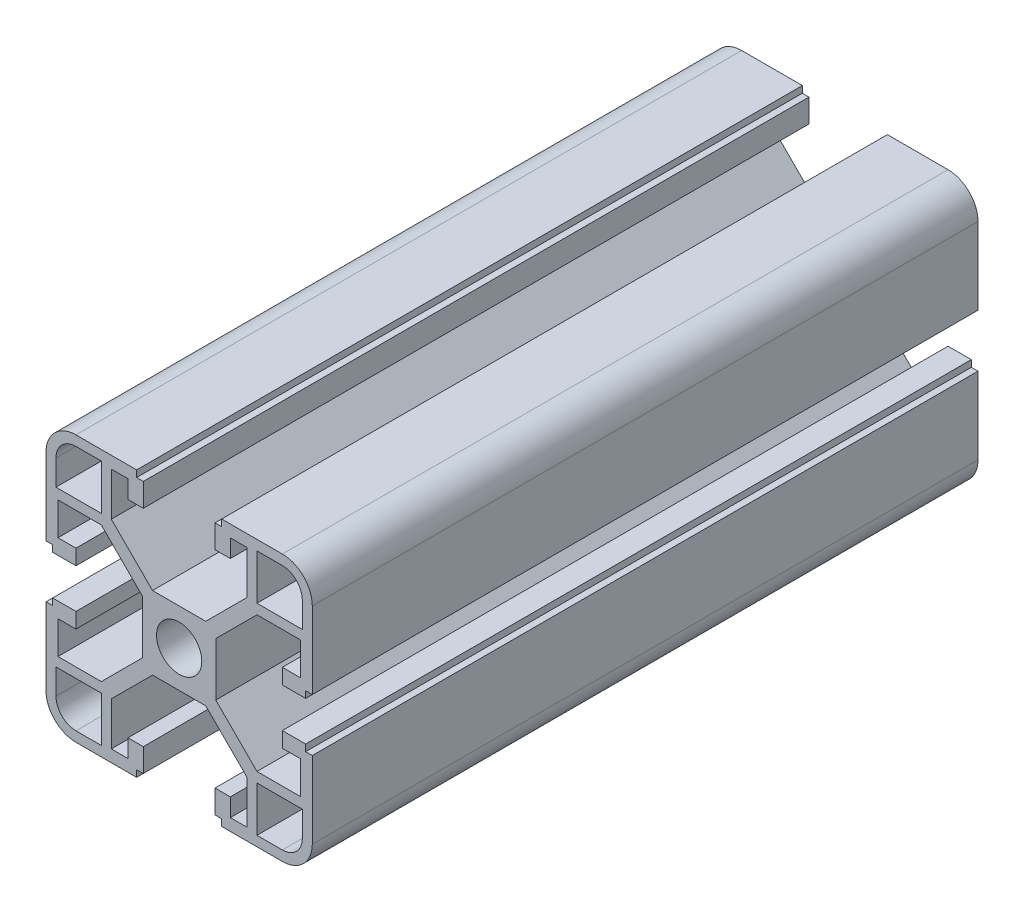
SolidWorks part; units mm, degrees
material "6061-T6 (SS)"
ref_plane "Front Plane" through (0, 0, 0) normal (0, 0, 1) x (1, 0, 0)
ref_plane "Top Plane" through (0, 0, 0) normal (0, 1, 0) x (1, 0, 0)
ref_plane "Right Plane" through (0, 0, 0) normal (1, 0, 0) x (0, 0, -1)
sketch "Sketch1" plane through (0, 0, 0) normal (0, 0, 1) x (1, 0, 0)
  line L0 (3.4, 0) -> (5.5, 0)
  line L1 (10.19, 11.69) -> (4, 5.5)
  line L2 (11.69, 10.19) -> (5.5, 4)
  line L3 (18.2, 10.19) -> (11.69, 10.19)
  line L4 (18.2, 10.19) -> (18.2, 5.2656)
  line L5 (18.2, 5.2656) -> (15.5, 5.2656)
  line L6 (15.5, 5.2656) -> (15.5, 2.9656)
  line L7 (15.5, 2.9656) -> (19, 2.9656)
  line L8 (19, 2.9656) -> (19, 3.9656)
  line L9 (19, 3.9656) -> (20, 3.9656)
  line L10 (20, 3.9656) -> (20, 15.5)
  line L11 (15.5, 20) -> (6.3853, 20)
  line L12 (18.5, 11.69) -> (18.5, 15.5)
  line L13 (15.5, 18.5) -> (11.69, 18.5)
  line L14 (11.69, 11.69) -> (11.69, 18.5)
  line L15 (0, 3.4) -> (0, 5.5)
  line L16 (4, 5.5) -> (0, 5.5)
  line L17 (6.3853, 20) -> (6.3853, 19)
  line L18 (5.5, 0) -> (5.5, 4)
  line L19 (6.3853, 19) -> (5.3853, 19)
  line L20 (5.3853, 19) -> (5.3853, 15.5)
  line L21 (5.3853, 15.5) -> (7.6853, 15.5)
  line L22 (10.19, 11.69) -> (10.19, 18.2)
  line L23 (11.69, 11.69) -> (18.5, 11.69)
  line L24 (7.6853, 18.2) -> (7.6853, 15.5)
  line L25 (10.19, 18.2) -> (7.6853, 18.2)
  arc A0 (20, 15.5) -> (15.5, 20) centre (15.5, 15.5) ccw
  arc A1 (18.5, 15.5) -> (15.5, 18.5) centre (15.5, 15.5) ccw
  arc A2 (3.4, 0) -> (0, 3.4) centre (0, 0) ccw
  dimension "D3" = 4.5
  dimension "D18" = 1.5
  dimension "D9" = 3.4
  dimension "D20" = 1.8
  dimension "D25" = 3
  dimension "D1" = 5.5
  dimension "D2" = 1.5
  dimension "D4" = 14.5
  dimension "D5" = 1.5
  dimension "D6" = 2.1
  dimension "D7" = 2.3
  dimension "D8" = 1.8
  dimension "D10" = 6.81
  dimension "D11" = 2.1
  dimension "D12" = 1
  dimension "D13" = 4.5
  dimension "D14" = 45
  dimension "D15" = 14.5
  dimension "D16" = 1
  dimension "D17" = 1.5
  dimension "D19" = 6.81
  dimension "D21" = 4.5
  dimension "D22" = 2.3
  dimension "D23" = 1
  dimension "D24" = 1
  dimension "D26" = 8.754
  dimension "D27" = 8.754
  dimension "D28" = 4.9244
  dimension "D29" = 2.5047
extrude "Boss-Extrude1" add sketch "Sketch1" along normal blind 100
mirror "Mirror1" about plane through (0, 0, 0) normal (0, 1, 0) of "Boss-Extrude1"
mirror "Mirror2" about plane through (0, 0, 0) normal (1, 0, 0) of "Boss-Extrude1"
mirror "Mirror3" about plane through (0, 0, 0) normal (0, 1, 0) of "Mirror2"
